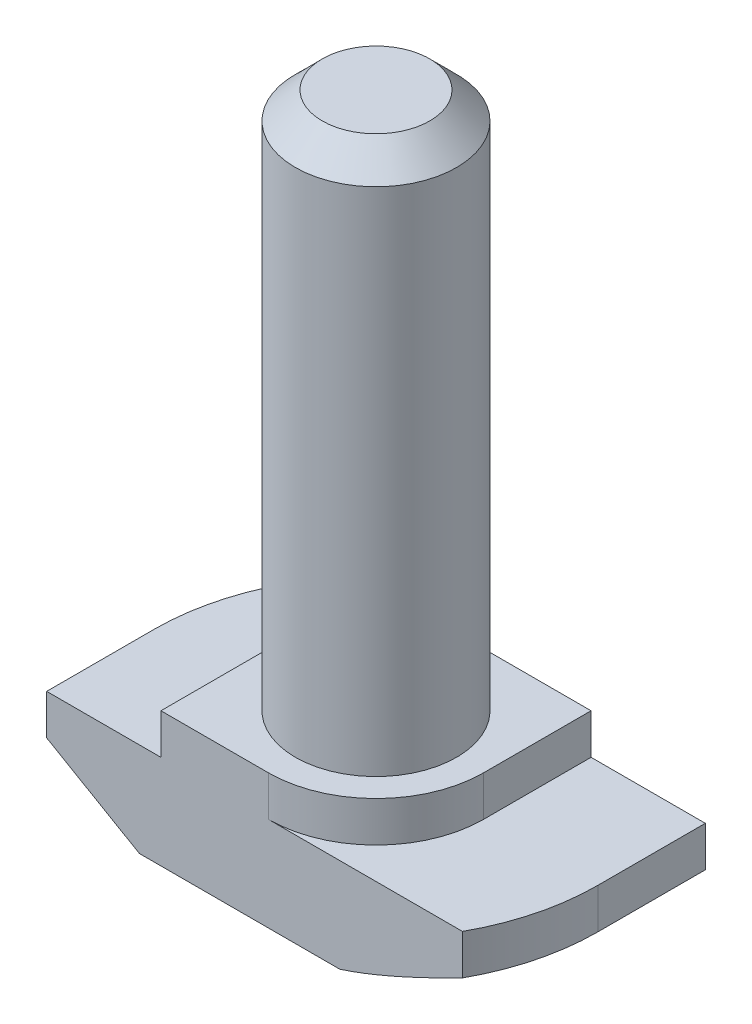
SolidWorks part; units mm, degrees
ref_plane "Спереди" through (0, 0, 0) normal (0, 0, 1) x (1, 0, 0)
ref_plane "Сверху" through (0, 0, 0) normal (0, 1, 0) x (1, 0, 0)
ref_plane "Справа" through (0, 0, 0) normal (1, 0, 0) x (0, 0, -1)
sketch "Эскиз1" plane through (0, 0, 0) normal (0, 0, 1) x (1, 0, 0)
  line L0 (8.25, 0) -> (-8.25, 0)
  line L1 (-8.25, 0) -> (-8.25, 3.5)
  line L2 (-8.25, 3.5) -> (-4, 3.5)
  line L3 (-4, 3.5) -> (-4, 5)
  line L4 (-4, 5) -> (4, 5)
  line L5 (0, 5) -> (0, 0) construction
  line L6 (4, 3.5) -> (4, 5)
  line L7 (8.25, 3.5) -> (4, 3.5)
  line L8 (8.25, 0) -> (8.25, 3.5)
  point P12 (-8.25, 2.6435)
  point P13 (-4, 3.6993)
  dimension "D1" = 8
  dimension "D2" = 16.5
  dimension "D3" = 5
  dimension "D4" = 1.5
extrude "Бобышка-Вытянуть1" add sketch "Эскиз1" along normal mid plane 8
sketch "Эскиз2" plane through (0, 5, 0) normal (0, 1, 0) x (1, 0, 0)
  circle A0 centre (0, 0) radius 3
  dimension "D1" = 6
extrude "Бобышка-Вытянуть2" add sketch "Эскиз2" along normal blind 20
cosmetic thread "Условное изображение резьбы1" parameters "D2"=4.891
sketch "Эскиз3" plane through (0, 5, 0) normal (0, 1, 0) x (1, 0, 0)
  line L0 (-4, -4) -> (-4, 4) construction
  line L1 (4, 4) -> (-4, 4) construction
  line L2 (-4, 0) -> (-4, 4)
  line L3 (-4, 4) -> (0, 4)
  line L4 (0, -4) -> (4, -4)
  line L5 (4, -4) -> (-4, -4) construction
  line L6 (4, -4) -> (4, 0)
  line L7 (4, -4) -> (4, 4) construction
  arc A0 (-4, 0) -> (0, 4) centre (0, 0) cw
  arc A1 (4, 0) -> (0, -4) centre (0, 0) cw
extrude "Вырез-Вытянуть1" cut sketch "Эскиз3" against normal up to surface (1.5 mm away) up to face at (-6.125, 3.5, 0)
sketch "Эскиз4" plane through (0, 3.5, 0) normal (0, 1, 0) x (1, 0, 0)
  line L0 (-8.25, -4) -> (-8.25, 4) construction
  line L1 (8.25, -4) -> (8.25, 4) construction
  line L2 (-7.2154, 4) -> (-8.25, 4)
  line L3 (-8.25, 4) -> (-8.25, 0)
  line L4 (7.2154, -4) -> (8.25, -4)
  line L5 (8.25, -4) -> (8.25, 0)
  arc A0 (-8.25, 0) -> (-7.2154, 4) centre (0, 0) cw
  arc A1 (8.25, 0) -> (7.2154, -4) centre (0, 0) cw
extrude "Вырез-Вытянуть2" cut sketch "Эскиз4" against normal through all
sketch "Эскиз5" plane through (0, 0, 4) normal (0, 0, 1) x (1, 0, 0)
  line L0 (-8.25, 2) -> (-4.8, 0)
  line L1 (-8.25, 3.5) -> (-8.25, 0) construction
  line L2 (-8.25, 0) -> (7.2154, 0) construction
  line L3 (-4.8, 0) -> (-8.25, 0)
  line L4 (-8.25, 0) -> (-8.25, 2)
  line L6 (-4, 3.5) -> (-8.25, 3.5) construction
  line L7 (-4, 5) -> (-4, 3.5) construction
  point P6 (-4.9519, 0)
  point P9 (0, 0)
  point P10 (-4.6154, 0)
  point P12 (-8.25, 2.2665)
  point P15 (0, 0)
  dimension "D1" = 1.5
  dimension "D2" = 0.8
sketch "Эскиз6" plane through (0, 0, 0) normal (0, -1, 0) x (1, 0, 0)
  line L0 (0, -8.25) -> (8.25, -8.25)
  line L1 (8.25, -8.25) -> (8.25, 0)
  line L2 (0, 8.25) -> (-8.25, 8.25)
  line L3 (-8.25, 8.25) -> (-8.25, 0)
  arc A0 (-8.25, 0) -> (0, -8.25) centre (0, 0) ccw
  arc A1 (8.25, 0) -> (0, 8.25) centre (0, 0) ccw
  point P10 (0, 0)
sweep "Вырез-По траектории1" cut profiles "Эскиз5" path "Эскиз6"
chamfer "Фаска2" distance 1 angle 45 1 edges at (0, 25, 3)
